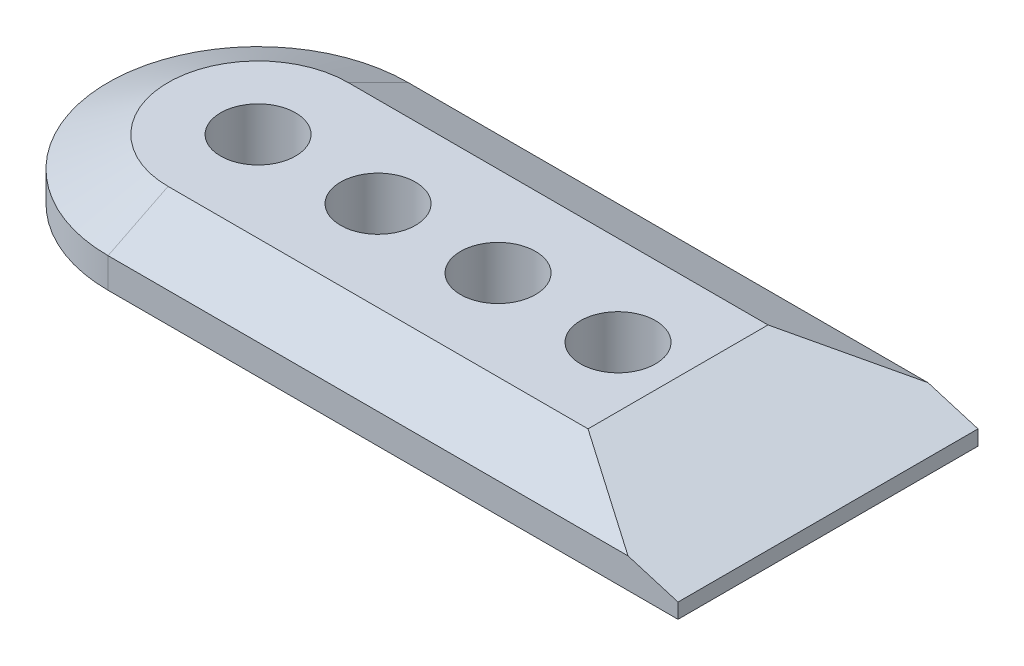
SolidWorks part; units mm, degrees
ref_plane "Front Plane" through (0, 0, 0) normal (0, 0, 1) x (1, 0, 0)
ref_plane "Top Plane" through (0, 0, 0) normal (0, 1, 0) x (1, 0, 0)
ref_plane "Right Plane" through (0, 0, 0) normal (1, 0, 0) x (0, 0, -1)
sketch "Sketch1" plane through (0, 0, 0) normal (0, 1, 0) x (1, 0, 0)
  line L0 (0, 31.75) -> (120.65, 31.75)
  line L1 (120.65, 31.75) -> (120.65, -31.75)
  line L2 (120.65, -31.75) -> (0, -31.75)
  arc A0 (0, -31.75) -> (0, 31.75) centre (0, 0) cw
  dimension "D1" = 31.75
  dimension "D2" = 120.65
extrude "Boss-Extrude1" add sketch "Sketch1" along normal blind 12.7 contours L0 L1 L2 A0
chamfer "Chamfer2" distance 12.7 distance2 6.35 3 edges at (60.325, 12.7, 31.75) (60.325, 12.7, -31.75) (-31.75, 12.7, 0)
chamfer "Chamfer3" distance 31.75 distance2 9.525 1 edges at (120.65, 12.7, 0)
sketch "Sketch2" plane through (0, 12.7, 0) normal (0, 1, 0) x (1, 0, 0)
  line L0 (0, 0) -> (25.4, 0) construction
  circle A0 centre (0, 0) radius 7.9375
  arc A1 (0, 31.75) -> (0, -31.75) centre (0, 0) ccw construction
  circle A2 centre (25.4, 0) radius 7.9375
  circle A3 centre (50.8, 0) radius 7.9375
  circle A4 centre (76.2, 0) radius 7.9375
  point P7 (-31.75, 0)
  dimension "D2" = 15.875
  dimension "D1" = 31.75
  dimension "D3" = 25.4
extrude "Cut-Extrude1" cut sketch "Sketch2" against normal through all
